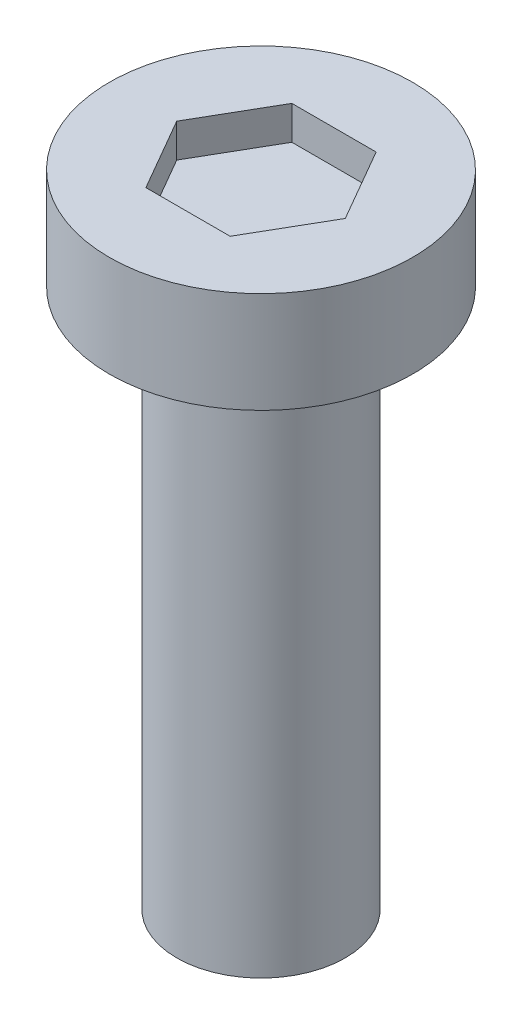
SolidWorks part; units mm, degrees
ref_plane "Front Plane" through (0, 0, 0) normal (0, 0, 1) x (1, 0, 0)
ref_plane "Top Plane" through (0, 0, 0) normal (0, 1, 0) x (1, 0, 0)
ref_plane "Right Plane" through (0, 0, 0) normal (1, 0, 0) x (0, 0, -1)
sketch "Sketch1" plane through (0, 0, 0) normal (0, 1, 0) x (1, 0, 0)
  circle A0 centre (0, 0) radius 1.25
  dimension "D1" = 2.5
extrude "Boss-Extrude1" add sketch "Sketch1" along normal blind 8
sketch "Sketch4" plane through (0, 8, 0) normal (0, 1, 0) x (1, 0, 0)
  circle A0 centre (0, 0) radius 2.25
  dimension "D1" = 4.5
extrude "Boss-Extrude2" add sketch "Sketch4" along normal blind 1.5
sketch "Sketch5" plane through (0, 9.5, 0) normal (0, 1, 0) x (1, 0, 0)
  line L1 (1.25, 0) -> (0.625, 1.0825)
  line L2 (0.625, 1.0825) -> (-0.625, 1.0825)
  line L3 (-0.625, 1.0825) -> (-1.25, 0)
  line L4 (-1.25, 0) -> (-0.625, -1.0825)
  line L5 (-0.625, -1.0825) -> (0.625, -1.0825)
  line L6 (0.625, -1.0825) -> (1.25, 0)
  circle A0 centre (0, 0) radius 1.0825 construction
  dimension "D1" = 1.25
extrude "Cut-Extrude1" cut sketch "Sketch5" against normal blind 0.5
thread "Thread1" pitch 0.7 start angle 0, offset 0, length 7, pitch 0.7, diameter 2.5
ref_plane "Plane1" through (1.25, 0, 0) normal (0, 0, 1) x (1, 0, 0)
sketch "Thread Profile1" plane through (1.25, 0, 0) normal (0, 0, 1) x (1, 0, 0)
  line L0 (0, 0) -> (0, 0.7) construction
  line L1 (0, 0) -> (0.3789, 0.2187)
  line L2 (0.3789, 0.2187) -> (0.3789, 0.3062)
  line L3 (0.3789, 0.3062) -> (0, 0.525)
  line L4 (0.3789, 0.2625) -> (0, 0.2625) construction
  line L11 (0, 0) -> (0, 0.525)
  point P2 (0, 0)
  dimension "Pitch" = 0.7
  dimension "Profile_Angle" = 60
  dimension "Profile_Land" = 0.0875
  dimension "Profile_Height" = 0.3789
